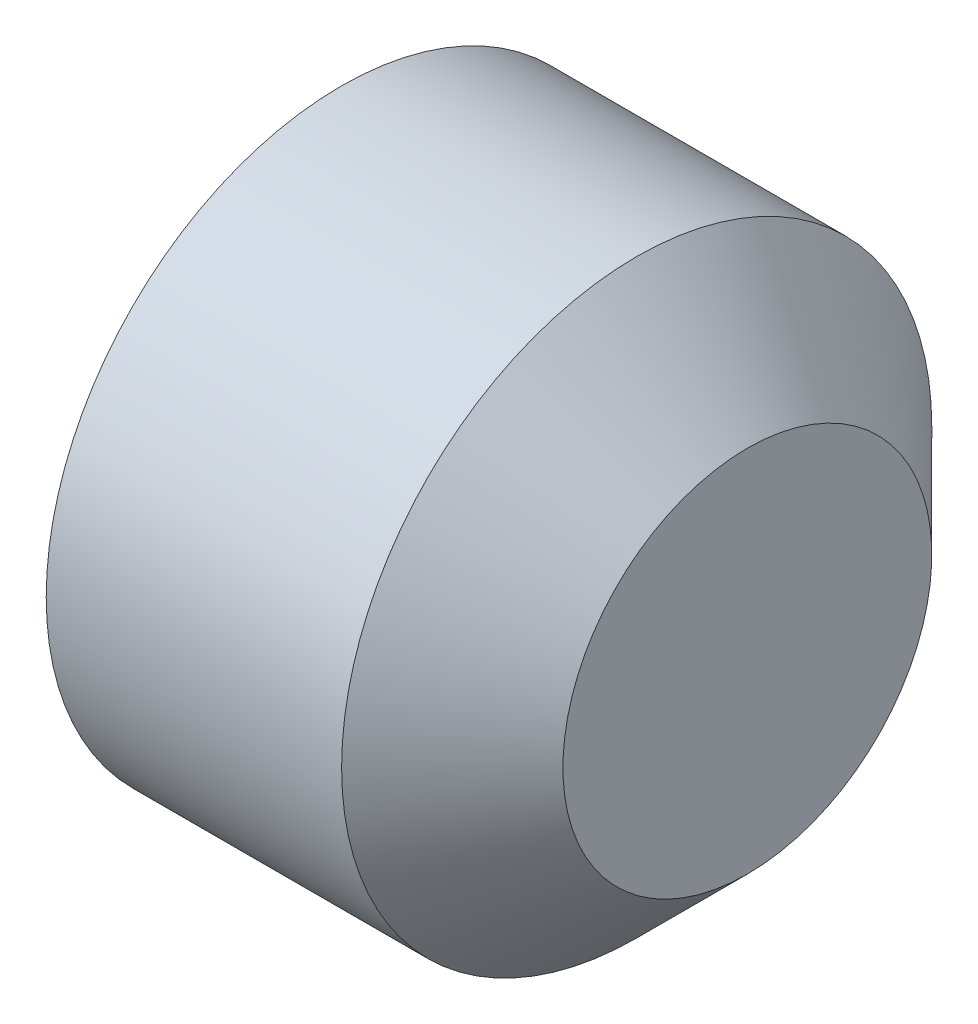
SolidWorks part; units mm, degrees
ref_plane "Front Plane" through (0, 0, 0) normal (0, 0, 1) x (1, 0, 0)
ref_plane "Top Plane" through (0, 0, 0) normal (0, 1, 0) x (1, 0, 0)
ref_plane "Right Plane" through (0, 0, 0) normal (1, 0, 0) x (0, 0, -1)
ref_plane "Plane1" through (0, 0, 0) normal (0, 0, 1) x (1, 0, 0)
sketch "Sketch1" plane through (0, 0, 0) normal (0, 0, 1) x (1, 0, 0)
  line L0 (3, 0) -> (3, -1.25)
  line L1 (3, -1.25) -> (2.25, -2)
  line L2 (2.25, -2) -> (0.248, -2)
  line L3 (0.248, -2) -> (0, -1.5705)
  line L4 (0, -1.5705) -> (0, -1.1547)
  line L5 (0, -1.1547) -> (0.6667, 0)
  line L6 (0.6667, 0) -> (3, 0)
  line L7 (0.6667, 0) -> (3, 0) construction
revolve "Revolve1" add sketch "Sketch1" angle 360 about L7
ref_plane "Plane2" through (0, 0, 0) normal (1, 0, 0) x (0, 0, -1)
sketch "Sketch2" plane through (0, 0, 0) normal (1, 0, 0) x (0, 0, -1)
  line L0 (-1.1547, 0) -> (-0.5774, -1)
  line L1 (-0.5774, -1) -> (0.5774, -1)
  line L2 (0.5774, -1) -> (1.1547, 0)
  line L3 (1.1547, 0) -> (0.5774, 1)
  line L4 (0.5774, 1) -> (-0.5774, 1)
  line L5 (-0.5774, 1) -> (-1.1547, 0)
extrude "Cut-Extrude1" cut sketch "Sketch2" along normal blind 1.5
